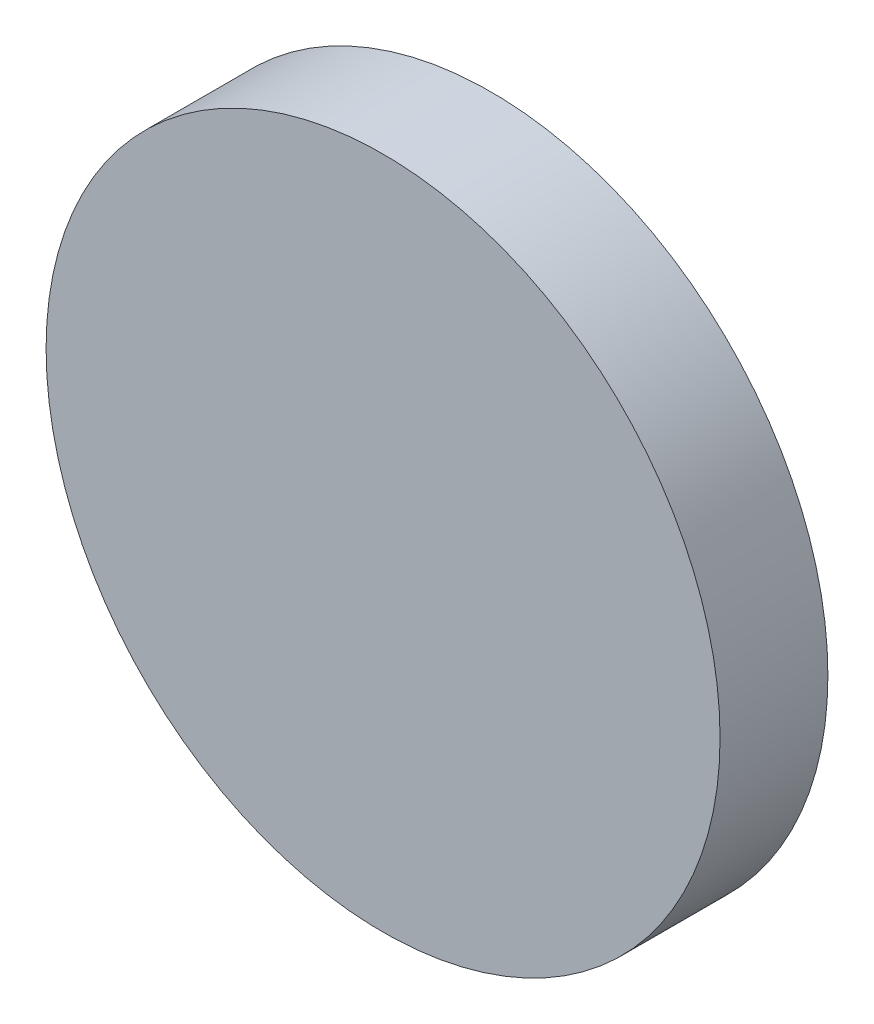
SolidWorks part; units mm, degrees
ref_plane "前视基准面" through (0, 0, 0) normal (0, 0, 1) x (1, 0, 0)
ref_plane "上视基准面" through (0, 0, 0) normal (0, 1, 0) x (1, 0, 0)
ref_plane "右视基准面" through (0, 0, 0) normal (1, 0, 0) x (0, 0, -1)
sketch "草图1" plane through (0, 0, 0) normal (0, 0, 1) x (1, 0, 0)
  circle A0 centre (0, 0) radius 6.25
  dimension "D1" = 12.5
extrude "凸台-拉伸1" add sketch "草图1" along normal blind 2 contours A0
